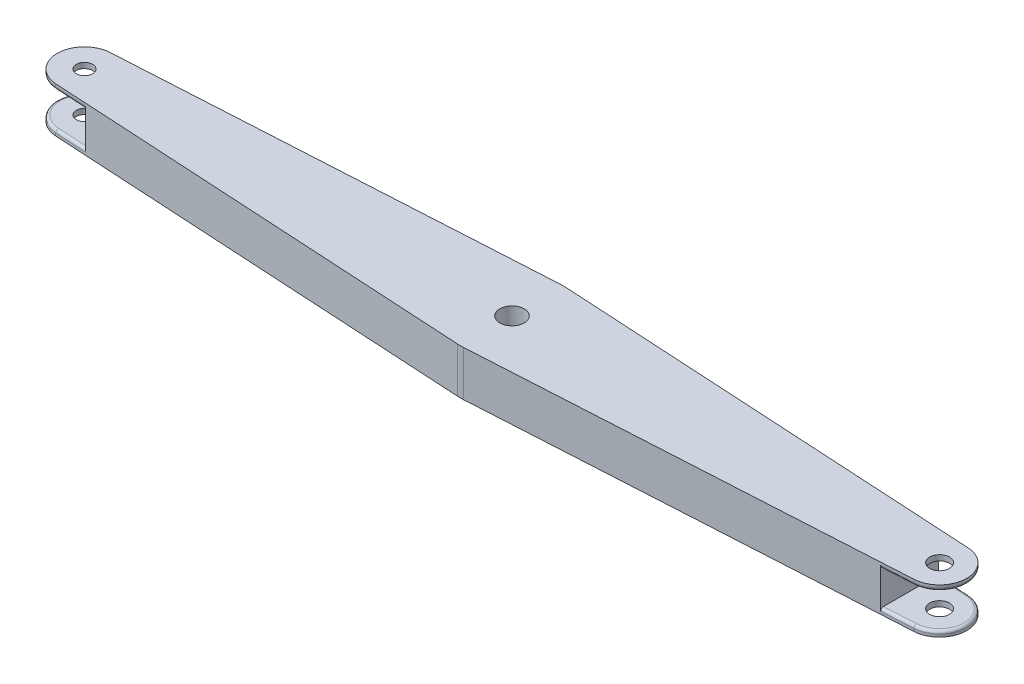
SolidWorks part; units mm, degrees
material "ABS"
ref_plane "Front Plane" through (0, 0, 0) normal (0, 0, 1) x (1, 0, 0)
ref_plane "Top Plane" through (0, 0, 0) normal (0, 1, 0) x (1, 0, 0)
ref_plane "Right Plane" through (0, 0, 0) normal (1, 0, 0) x (0, 0, -1)
sketch "Sketch1" plane through (0, 0, 0) normal (0, 1, 0) x (1, 0, 0)
  line L0 (-188.0647, 0) -> (188.0647, 0) construction
  line L1 (1.0871, 18.9689) -> (157.8722, 9.9836)
  line L2 (-1.0871, 18.9689) -> (-157.8722, 9.9836)
  line L3 (0, 0) -> (0, 122.8429) construction
  line L4 (-1.0871, -18.9689) -> (-157.8722, -9.9836)
  line L5 (1.0871, -18.9689) -> (157.8722, -9.9836)
  line L6 (0, 0) -> (0, -60.8855) construction
  circle A0 centre (0, 0) radius 18
  arc A1 (-1.0871, 18.9689) -> (1.0871, 18.9689) centre (0, 0) cw
  arc A2 (157.8722, 9.9836) -> (157.8722, -9.9836) centre (157.3, 0) cw
  arc A3 (-157.8722, 9.9836) -> (-157.8722, -9.9836) centre (-157.3, 0) ccw
  circle A4 centre (-157.3, 0) radius 3
  circle A5 centre (157.3, 0) radius 3.6282
  arc A6 (-1.0871, -18.9689) -> (1.0871, -18.9689) centre (0, 0) ccw
  point P8 (0, 0)
  point P16 (0, 19)
  dimension "D1" = 36
  dimension "D6" = 3
  dimension "D7" = 3.6282
  dimension "D2" = 10
  dimension "D3" = 10
  dimension "D4" = 19
  dimension "D5" = 157.3
  dimension "D8" = 157.3
extrude "Boss-Extrude1" add sketch "Sketch1" along normal blind 16.65 contours A0 | L4 A6 L5 A2 L1 A1 L2 A3 A0 A4 A5
ref_plane "Plane1" through (-157.3, 0, 0) normal (1, 0, 0) x (0, 0, -1)
sketch "Sketch2" plane through (-157.3, 0, 0) normal (1, 0, 0) x (0, 0, -1)
  line L0 (0, 16.65) -> (0, 0) construction
  line L1 (15, 2) -> (-15, 2)
  line L2 (15, 2) -> (15, 14.65)
  line L3 (15, 14.65) -> (-15, 14.65)
  line L4 (-15, 2) -> (-15, 14.65)
  line L5 (15, 2) -> (-15, 14.65) construction
  line L6 (15, 14.65) -> (-15, 2) construction
  point P0 (0, 8.325)
  dimension "D1" = 12.65
  dimension "D2" = 30
extrude "Cut-Extrude2" cut sketch "Sketch2" against normal mid plane 22
mirror "Mirror1" about plane through (0, 0, 0) normal (1, 0, 0) of "Cut-Extrude2"
sketch "Sketch3" plane through (0, 16.65, 0) normal (0, 1, 0) x (1, 0, 0)
  circle A0 centre (0, 0) radius 4.5
  dimension "D1" = 9
extrude "Cut-Extrude3" cut sketch "Sketch3" against normal up to next
fillet "Fillet2" radius 1 12 edges at (-152.0861, 2, 10.3152) (-152.0861, 2, -10.3152) (-167.3, 2, 0) (152.0861, 14.65, 10.3152) (152.0861, 14.65, -10.3152) (152.0861, 2, -10.3152) (152.0861, 2, 10.3152) (-152.0861, 14.65, -10.3152) (-152.0861, 14.65, 10.3152) (167.3, 14.65, 0) (167.3, 2, 0) (-167.3, 14.65, 0)
